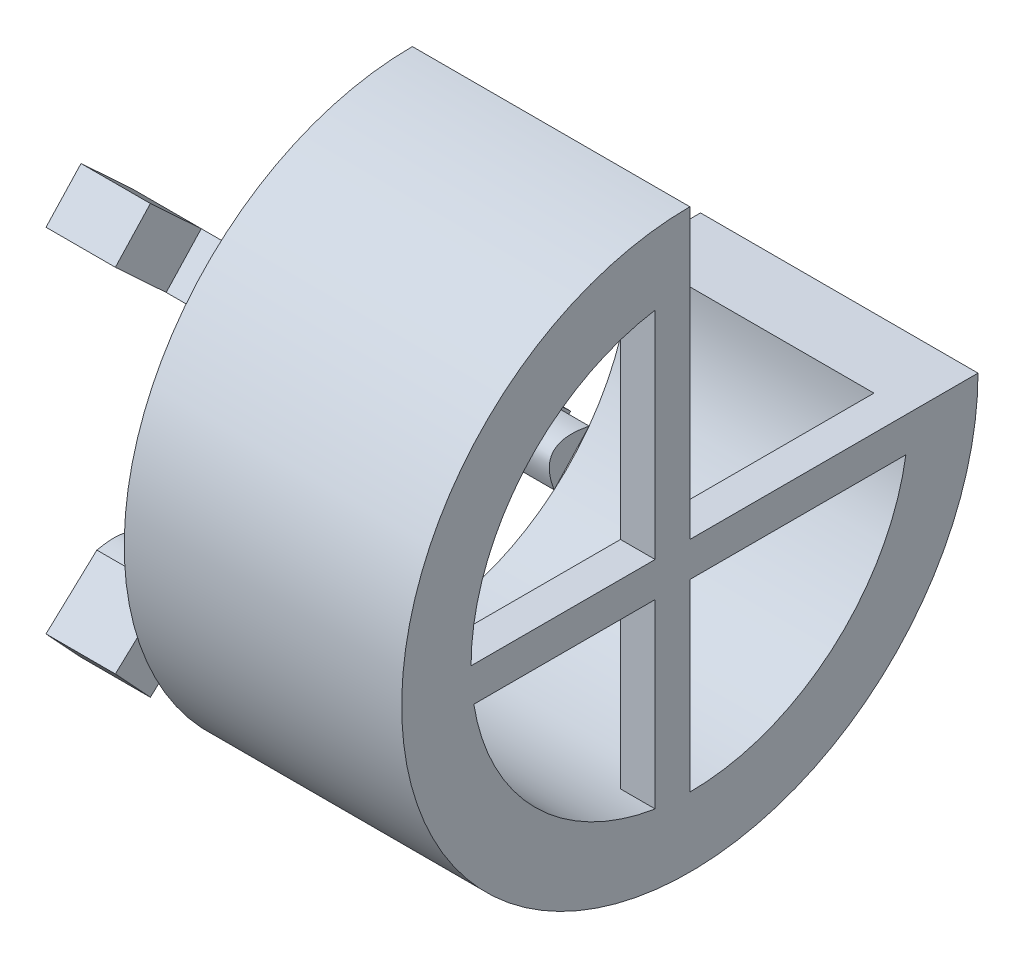
SolidWorks part; units mm, degrees
material "PP Copolymer"
ref_plane "Front Plane" through (0, 0, 0) normal (0, 0, 1) x (1, 0, 0)
ref_plane "Top Plane" through (0, 0, 0) normal (0, 1, 0) x (1, 0, 0)
ref_plane "Right Plane" through (0, 0, 0) normal (1, 0, 0) x (0, 0, -1)
sketch "Sketch1" plane through (0, 0, 0) normal (0, 0, 1) x (1, 0, 0)
  line L0 (-37.2885, 0) -> (42.3192, 0) construction
  line L1 (0, 28.6748) -> (0, -24.072) construction
  line L2 (42.3192, 20.77) -> (-41.9611, 20.77) construction
  line L3 (42.3192, 15.77) -> (-41.9611, 15.77) construction
  line L4 (42.3192, -15.77) -> (-46.4732, -15.77) construction
  line L5 (43.6399, -20.77) -> (20, -20.77) construction
  line L6 (20, 20.77) -> (0, 20.77)
  line L7 (20, 20.77) -> (20, 15.77)
  line L8 (0, -20.77) -> (-47.5045, -20.77) construction
  line L9 (0, 20.77) -> (0, 15.77)
  line L10 (20, 15.77) -> (0, 15.77)
  dimension "D3" = 20
revolve "Revolve1" add sketch "Sketch1" angle 270 about L0
sketch "Sketch2" plane through (20, 0, 0) normal (1, 0, 0) x (0, 0, -1)
  line L0 (0, 20.77) -> (0, -20.77)
  line L1 (0, 6.8774) -> (-2.5, 6.8774) construction
  line L2 (-2.5, 20.619) -> (-2.5, -20.619)
  line L3 (20.77, 0) -> (-20.77, 0)
  line L4 (-1.25, 0) -> (-1.25, -2.5) construction
  line L5 (-20.619, -2.5) -> (20.619, -2.5)
  arc A0 (-20.619, -2.5) -> (-20.77, 0) centre (0, 0) cw
  arc A1 (0, 20.77) -> (20.77, 0) centre (0, 0) ccw construction
  arc A2 (20.77, 0) -> (20.619, -2.5) centre (0, 0) cw
  arc A3 (-2.5, -20.619) -> (0, -20.77) centre (0, 0) ccw
  arc A4 (-2.5, 20.619) -> (0, 20.77) centre (0, 0) cw
  dimension "D3" = 20.77
  dimension "D4" = 20.77
  dimension "D1" = 2.5
  dimension "D2" = 2.5
extrude "Boss-Extrude1" add sketch "Sketch2" against normal blind 2.5 contours A2 L5 A0 L3 | A4 L0 A3 L2
sketch "Sketch4" plane through (0, 0, 0) normal (1, 0, 0) x (0, 0, -1)
  line L0 (0, 22.6692) -> (0, -27.8926) construction
  line L1 (24.2362, 0) -> (-49.5171, 0) construction
  spline S0 degree 2 poles (-12.7423, 9.2912) (-8.866, 8.4937) (-10.2186, 12.0114) knots 0 0 0 1 1 1
  spline S1 degree 2 poles (-12.7423, -9.2912) (-8.866, -8.4937) (-10.2186, -12.0114) knots 0 0 0 1 1 1
  spline S2 degree 1 poles (-10.2186, 12.0114) (-12.7423, 9.2912) knots 0 0 1 1
  spline S3 degree 2 poles (12.7423, -9.2912) (8.866, -8.4937) (10.2186, -12.0114) knots 0 0 0 1 1 1
  spline S4 degree 1 poles (-10.2186, -12.0114) (-12.7423, -9.2912) knots 0 0 1 1
  spline S5 degree 1 poles (10.2186, -12.0114) (12.7423, -9.2912) knots 0 0 1 1
extrude "Boss-Extrude2" add sketch "Sketch4" against normal blind 10 separate body
sketch "Sketch5" plane through (0, -10.6513, -11.4804) normal (0, -0.6801, -0.7331) x (-1, 0, 0)
  line L0 (10, 1.8553) -> (5, 1.8553)
  line L1 (5, 1.8553) -> (5, -1.8553)
  line L2 (10, 1.8553) -> (0, 1.8553) construction
  line L3 (10, -1.8553) -> (0, -1.8553) construction
  line L4 (5, -1.8553) -> (10, -1.8553)
  line L5 (10, -1.8553) -> (10, 1.8553)
  dimension "D1" = 5
extrude "Boss-Extrude3" add sketch "Sketch5" along normal blind 5
sketch "Sketch6" plane through (0, -10.6513, 11.4804) normal (0, -0.6801, 0.7331) x (1, 0, 0)
  line L0 (-10, -1.8553) -> (-5, -1.8553)
  line L2 (-10, -1.8553) -> (0, -1.8553) construction
  line L3 (-5, -1.8553) -> (-5, 1.8553)
  line L4 (-10, 1.8553) -> (0, 1.8553) construction
  line L5 (-5, 1.8553) -> (-10, 1.8553)
  line L6 (-10, 1.8553) -> (-10, -1.8553)
  dimension "D1" = 5
extrude "Boss-Extrude4" add sketch "Sketch6" along normal blind 5
sketch "Sketch7" plane through (0, 10.6513, 11.4804) normal (0, 0.6801, 0.7331) x (1, 0, 0)
  line L0 (-10, -1.8553) -> (-5, -1.8553)
  line L2 (-10, -1.8553) -> (0, -1.8553) construction
  line L3 (-5, -1.8553) -> (-5, 1.8553)
  line L4 (-5, 1.8553) -> (-10, 1.8553)
  line L5 (-10, 1.8553) -> (-10, -1.8553)
  dimension "D1" = 5
extrude "Boss-Extrude5" add sketch "Sketch7" along normal blind 5
